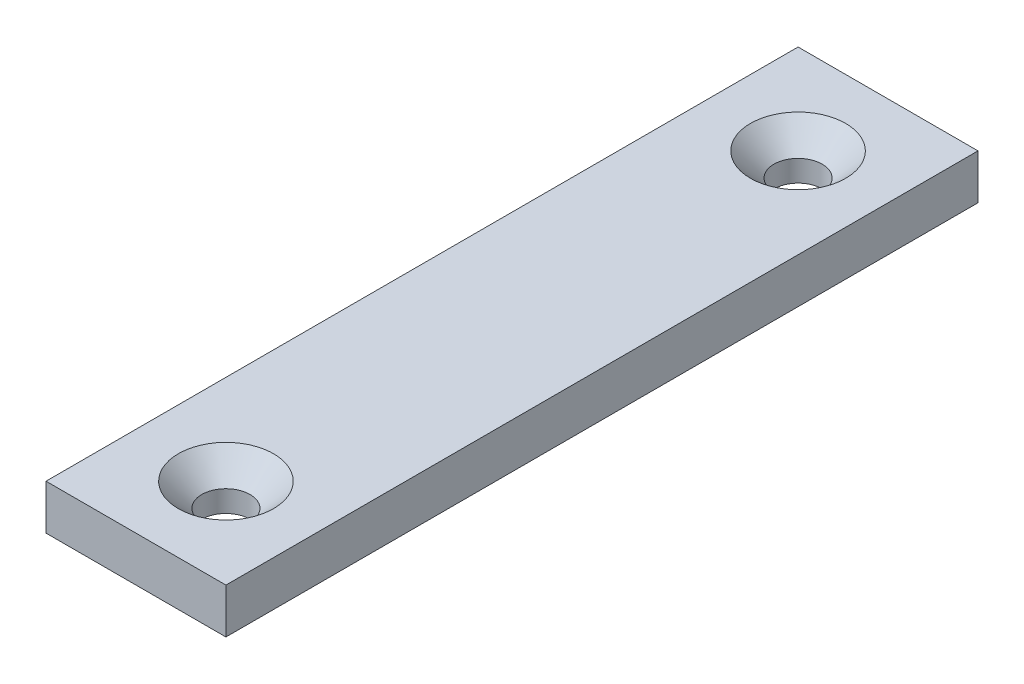
SolidWorks part; units mm, degrees
material "Copper"
ref_plane "Front Plane" through (0, 0, 0) normal (0, 0, 1) x (1, 0, 0)
ref_plane "Top Plane" through (0, 0, 0) normal (0, 1, 0) x (1, 0, 0)
ref_plane "Right Plane" through (0, 0, 0) normal (1, 0, 0) x (0, 0, -1)
sketch "Sketch1" plane through (0, 0, 0) normal (0, 1, 0) x (1, 0, 0)
  line L1 (0, 0) -> (12.7, 0)
  line L2 (0, 0) -> (0, 53.086)
  line L3 (0, 53.086) -> (12.7, 53.086)
  line L4 (12.7, 0) -> (12.7, 53.086)
  dimension "D1" = 12.7
  dimension "D2" = 53.086
extrude "Boss-Extrude1" add sketch "Sketch1" along normal blind 3.175
hole_wizard "CSK for M3 SFHCS1" positions "Sketch3" profile "Sketch2" countersink size "M3" standard "ANSI Metric" end condition through all
sketch "Sketch3" plane through (0, 3.175, 0) normal (0, 1, 0) x (1, 0, 0)
  line L0 (6.35, 0) -> (6.35, 53.086) construction
  line L1 (0, 0) -> (12.7, 0) construction
  line L2 (12.7, 53.086) -> (0, 53.086) construction
  point P7 (6.35, 6.35)
  point P9 (6.35, 46.736)
  dimension "D1" = 6.35
  dimension "D2" = 6.35
sketch "Sketch2" plane through (6.35, 3.175, -6.35) normal (1, 0, 0) x (0, 0, 1)
  line L0 (0, 0) -> (0, 3.175)
  line L1 (0, 3.175) -> (1.7, 3.175)
  line L2 (1.7, 3.175) -> (1.7, 1.66)
  line L3 (1.7, 1.66) -> (3.36, 0)
  line L5 (3.36, 0) -> (0, 0)
  line L6 (-1.7, 1.66) -> (-3.36, 0) construction
  line L11 (0, -6.35) -> (0, 107.95) construction
  dimension "Thru Hole Dia." = 3.4
  dimension "Thru Hole Depth" = 3.175
  dimension "Near C'Sink Dia." = 6.72
  dimension "Near C'Sink Angle" = 90
equation "\"ABS_thickness\" = 1.59\t"
equation "\"Bus_bar_thickness\" = 3.175"
equation "\"Connector_width\" = 20.2"
equation "\"Number_of_cells_long\" = 25"
equation "\"Number_of_cells_wide\" = 2"
equation "\"Cell_height\" = 65.0"
equation "\"Cell_diam\" = 18.0"
equation "\"D1@Boss-Extrude1\"=\"Bus_bar_thickness\""
equation "\"D1@Sketch3\"=12.7/2"
equation "\"D2@Sketch3\"=\"D1@Sketch3\""
